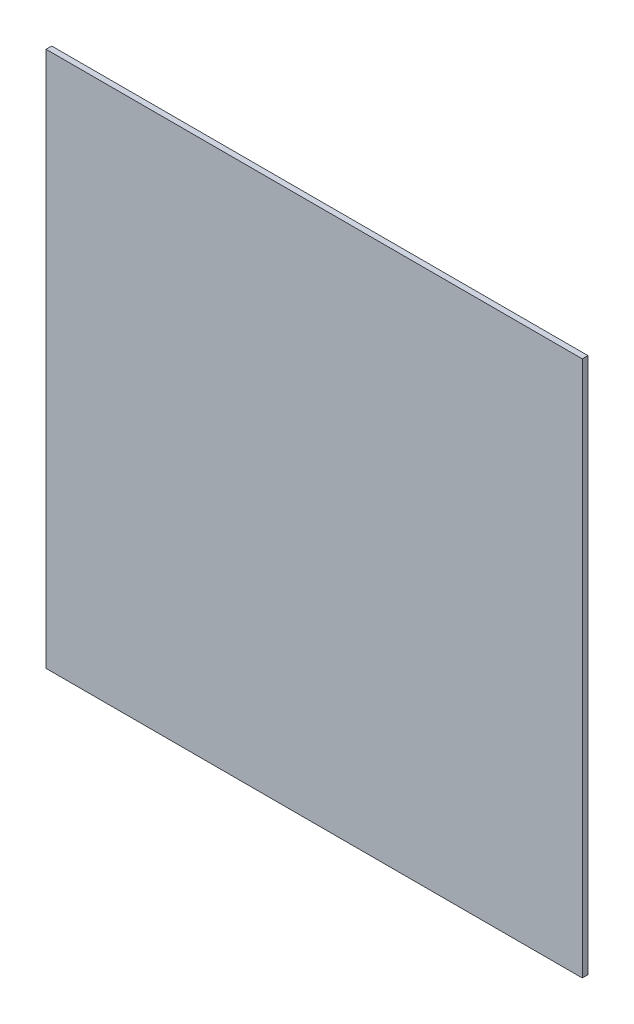
SolidWorks part; units mm, degrees
material "Glass"
ref_plane "Front Plane" through (0, 0, 0) normal (0, 0, 1) x (1, 0, 0)
ref_plane "Top Plane" through (0, 0, 0) normal (0, 1, 0) x (1, 0, 0)
ref_plane "Right Plane" through (0, 0, 0) normal (1, 0, 0) x (0, 0, -1)
sketch "Sketch1" plane through (0, 0, 0) normal (0, 0, 1) x (1, 0, 0)
  line L0 (150, 150) -> (-150, -150) construction
  line L1 (-150, 150) -> (150, 150)
  line L2 (-150, 150) -> (-150, -150)
  line L3 (-150, -150) -> (150, -150)
  line L4 (150, 150) -> (150, -150)
  dimension "D1" = 300
extrude "Boss-Extrude1" add sketch "Sketch1" along normal blind 3.175
